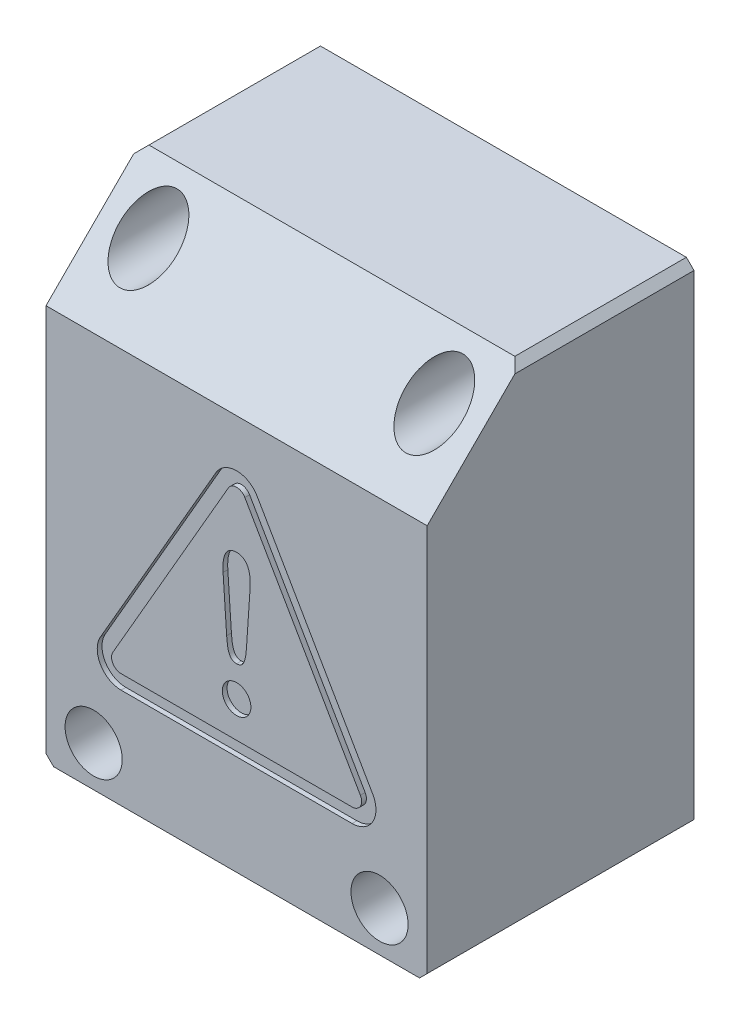
SolidWorks part; units mm, degrees
ref_plane "Front Plane" through (0, 0, 0) normal (0, 0, 1) x (1, 0, 0)
ref_plane "Top Plane" through (0, 0, 0) normal (0, 1, 0) x (1, 0, 0)
ref_plane "Right Plane" through (0, 0, 0) normal (1, 0, 0) x (0, 0, -1)
ref_plane "Plane1" through (19.8609, 0, 0) normal (1, 0, 0) x (0, 0, -1)
sketch "Sketch1" plane through (19.8609, 0, 0) normal (1, 0, 0) x (0, 0, -1)
  line L0 (0.0201, -25.9091) -> (0.0201, 25.5909)
  line L1 (0.0201, 25.5909) -> (-17.9799, 25.5909)
  line L2 (-17.9799, 25.5909) -> (-27.9799, 15.5909)
  line L3 (-27.9799, 15.5909) -> (-27.9799, -25.9091)
  line L4 (-27.9799, -25.9091) -> (0.0201, -25.9091)
  dimension "D1" = 10
  dimension "D2" = 28
  dimension "D3" = 41.5
  dimension "D4" = 51.5
extrude "Boss-Extrude1" add sketch "Sketch1" against normal blind 40
ref_plane "Plane2" through (-19.1391, 0, 0) normal (-1, 0, 0) x (0, -1, 0)
sketch "Sketch2" plane through (-19.1391, 0, 0) normal (-1, 0, 0) x (0, -1, 0)
  line L0 (-24.5909, 17.5657) -> (-24.5909, -0.0201)
  line L1 (-24.5909, -0.0201) -> (24.9091, -0.0201)
  line L2 (24.9091, -0.0201) -> (24.9091, 26.9799)
  line L3 (24.9091, 26.9799) -> (-15.1767, 26.9799)
  line L4 (-15.1767, 26.9799) -> (-24.5909, 17.5657)
  dimension "D1" = 9.4142
  dimension "D2" = 49.5
  dimension "D3" = 17.5858
  dimension "D4" = 27
extrude "Cut-Extrude1" cut sketch "Sketch2" against normal blind 38
sketch "Sketch3" plane through (18.8609, 0, 0) normal (-1, 0, 0) x (0, 0, 1)
  line L0 (-0.0201, 10.3409) -> (-0.0201, 3.8409)
  line L1 (-0.0201, 3.8409) -> (18.9799, 3.8409)
  line L2 (18.9799, 3.8409) -> (18.9799, 10.3409)
  line L3 (18.9799, 10.3409) -> (-0.0201, 10.3409)
  line L5 (17.5657, 24.5909) -> (-0.0201, 24.5909) construction
  line L6 (-0.0201, 24.5909) -> (-0.0201, -24.9091) construction
  dimension "D1" = 19
  dimension "D2" = 14.25
  dimension "D3" = 20.75
extrude "Cut-Extrude2" [suppressed] cut sketch "Sketch3" against normal through all
sketch "Sketch4" plane through (-20.1391, 0, 0) normal (-1, 0, 0) x (0, 0, 1)
  line L0 (-0.0201, 3.8409) -> (18.9799, 3.8409)
  line L1 (18.9799, 3.8409) -> (18.9799, 10.3409)
  line L2 (18.9799, 10.3409) -> (-0.0201, 10.3409)
  line L3 (-0.0201, 10.3409) -> (-0.0201, 3.8409)
  line L4 (27.9799, -25.9091) -> (-0.0201, -25.9091) construction
  line L5 (27.9799, 15.5909) -> (27.9799, -25.9091) construction
  dimension "D1" = 9
  dimension "D2" = 28
  dimension "D3" = 29.75
  dimension "D4" = 36.25
extrude "Cut-Extrude3" [suppressed] cut sketch "Sketch4" against normal through all
ref_plane "Plane3" through (0, 21.0783, 21.0783) normal (0, 0.7071, 0.7071) x (-1, 0, 0)
ref_plane "Plane4" through (0, 0, 7.9799) normal (0, 0, -1) x (-1, 0, 0)
sketch "Sketch6" plane through (0, 0, 7.9799) normal (0, 0, -1) x (-1, 0, 0)
  line L0 (19.1391, 24.5909) -> (11.1391, 24.5909)
  line L1 (11.1391, 24.5909) -> (11.1391, 17.3409)
  line L2 (11.1391, 17.3409) -> (19.1391, 17.3409)
  line L3 (19.1391, 17.3409) -> (19.1391, 24.5909)
  dimension "D1" = 8
  dimension "D2" = 7.25
extrude "Boss-Extrude2" add sketch "Sketch6" against normal up to surface up to plane "Plane3"
sketch "Sketch7" plane through (0, 0, 7.9799) normal (0, 0, -1) x (-1, 0, 0)
  line L0 (-18.8609, 24.5909) -> (-18.8609, 17.3409)
  line L1 (-18.8609, 17.3409) -> (-10.8609, 17.3409)
  line L2 (-10.8609, 17.3409) -> (-10.8609, 24.5909)
  line L3 (-10.8609, 24.5909) -> (-18.8609, 24.5909)
  dimension "D1" = 8
  dimension "D2" = 7.25
extrude "Boss-Extrude3" add sketch "Sketch7" against normal up to next
sketch "Sketch8" plane through (0, 0, 26.9799) normal (0, 0, -1) x (-1, 0, 0)
  line L0 (-10.8609, -24.9091) -> (-18.8609, -24.9091)
  line L1 (-18.8609, -24.9091) -> (-18.8609, -17.6591)
  line L2 (-18.8609, -17.6591) -> (-10.8609, -17.6591)
  line L3 (-10.8609, -17.6591) -> (-10.8609, -24.9091)
  line L4 (19.1391, -24.9091) -> (19.1391, 15.1767) construction
  line L5 (-18.8609, 15.1767) -> (19.1391, 15.1767) construction
  dimension "D1" = 30
  dimension "D2" = 38
  dimension "D3" = 32.8358
  dimension "D4" = 40.0858
extrude "Boss-Extrude4" add sketch "Sketch8" along normal blind 19
sketch "Sketch9" plane through (0, 0, 26.9799) normal (0, 0, -1) x (-1, 0, 0)
  line L0 (19.1391, -17.6591) -> (19.1391, -24.9091)
  line L1 (19.1391, -24.9091) -> (11.1391, -24.9091)
  line L2 (11.1391, -24.9091) -> (11.1391, -17.6591)
  line L3 (11.1391, -17.6591) -> (19.1391, -17.6591)
  line L4 (19.1391, -24.9091) -> (19.1391, 15.1767) construction
  line L5 (-10.8609, -24.9091) -> (19.1391, -24.9091) construction
  dimension "D1" = 8
  dimension "D2" = 7.25
extrude "Boss-Extrude5" add sketch "Sketch9" along normal blind 19
sketch "Sketch10" plane through (0, 0, 27.9799) normal (0, 0, 1) x (1, 0, 0)
  line L0 (14.1503, -11.6591) -> (2.0259, 9.3409)
  line L1 (-2.3042, 9.3409) -> (-14.4285, -11.6591)
  line L2 (-12.2635, -15.4091) -> (11.9852, -15.4091)
  line L3 (19.8609, 15.5909) -> (19.8609, -25.9091) construction
  line L4 (-20.1391, 15.5909) -> (19.8609, 15.5909) construction
  arc A0 (11.9852, -15.4091) -> (14.1503, -11.6591) centre (11.9852, -12.9091) ccw
  arc A1 (2.0259, 9.3409) -> (-2.3042, 9.3409) centre (-0.1391, 8.0909) ccw
  arc A2 (-14.4285, -11.6591) -> (-12.2635, -15.4091) centre (-12.2635, -12.9091) ccw
  dimension "D1" = 2.5
  dimension "D2" = 2.5
  dimension "D3" = 5.7106
  dimension "D4" = 7.8756
  dimension "D5" = 17.8349
  dimension "D6" = 6.25
extrude "Cut-Extrude4" cut sketch "Sketch10" against normal blind 0.5
sketch "Sketch11" plane through (0, 0, 27.4799) normal (0, 0, 1) x (1, 0, 0)
  line L0 (-13.1295, -12.4091) -> (-1.0052, 8.5909)
  line L1 (0.7269, 8.5909) -> (12.8513, -12.4091)
  line L2 (11.9852, -13.9091) -> (-12.2635, -13.9091)
  arc A0 (-1.0052, 8.5909) -> (0.7269, 8.5909) centre (-0.1391, 8.0909) cw
  arc A1 (12.8513, -12.4091) -> (11.9852, -13.9091) centre (11.9852, -12.9091) cw
  arc A2 (-12.2635, -13.9091) -> (-13.1295, -12.4091) centre (-12.2635, -12.9091) cw
  dimension "D1" = 1
  dimension "D2" = 1
  dimension "D3" = 1.299
  dimension "D4" = 2.1651
  dimension "D5" = 14.2894
  dimension "D6" = 0.75
extrude "Boss-Extrude6" add sketch "Sketch11" along normal blind 0.5
ref_plane "Plane5" through (0, 0, 26.4799) normal (0, 0, 1) x (1, 0, 0)
sketch "Sketch12" plane through (0, 0, 26.4799) normal (0, 0, 1) x (1, 0, 0)
  line L0 (-1.1818, -4.92) -> (-1.5574, 0.6422)
  line L1 (1.2791, 0.6422) -> (0.9035, -4.92)
  spline S0 degree 3 poles (-1.5574, 0.6422) (-1.5623, 0.7269) (-1.572, 0.8961) (-1.5736, 1.1504) (-1.5635, 1.4044) (-1.5395, 1.6575) (-1.4986, 1.9084) (-1.436, 2.155) (-1.3478, 2.3942) (-1.2279, 2.6201) (-1.0702, 2.8215) (-0.8738, 2.9864) (-0.6445, 3.1009) (-0.3955, 3.1666) (-0.2248, 3.1736) (-0.1391, 3.1771) knots 0 0 0 0 0.076934 0.153716 0.23049 0.30738 0.384178 0.460862 0.537778 0.614836 0.691826 0.768406 0.845421 0.922433 1 1 1 1
  spline S1 degree 3 poles (-0.1391, 3.1771) (-0.0655, 3.1745) (0.0814, 3.1695) (0.2981, 3.1217) (0.5034, 3.0377) (0.689, 2.9145) (0.8467, 2.7573) (0.9749, 2.5757) (1.0751, 2.3781) (1.1517, 2.1705) (1.2085, 1.957) (1.2488, 1.7403) (1.2753, 1.5222) (1.2903, 1.303) (1.2954, 1.083) (1.2921, 0.8626) (1.2834, 0.7157) (1.2791, 0.6422) knots 0 0 0 0 0.06669 0.133119 0.19992 0.266795 0.333669 0.400734 0.467442 0.534072 0.600968 0.667508 0.733796 0.800116 0.866607 0.933255 1 1 1 1
  spline S2 degree 3 poles (0.9035, -4.92) (0.899, -4.9847) (0.89, -5.114) (0.8736, -5.3078) (0.8534, -5.5013) (0.8284, -5.6943) (0.7967, -5.8864) (0.7549, -6.0766) (0.7007, -6.2637) (0.6289, -6.4449) (0.5329, -6.6149) (0.4053, -6.7638) (0.2432, -6.8747) (0.0564, -6.939) (-0.0737, -6.9455) (-0.1391, -6.9488) knots 0 0 0 0 0.076937 0.153837 0.230708 0.307639 0.384652 0.461589 0.538535 0.615507 0.692327 0.76911 0.845963 0.922602 1 1 1 1
  spline S3 degree 3 poles (-0.1391, -6.9488) (-0.2042, -6.9456) (-0.3345, -6.9393) (-0.5217, -6.8747) (-0.6846, -6.7631) (-0.8124, -6.6132) (-0.9083, -6.4425) (-0.9801, -6.2606) (-1.034, -6.0733) (-1.0756, -5.8833) (-1.1071, -5.6919) (-1.1318, -5.4998) (-1.1519, -5.3069) (-1.1683, -5.1136) (-1.1773, -4.9845) (-1.1818, -4.92) knots 0 0 0 0 0.076984 0.154213 0.231303 0.308509 0.385703 0.462682 0.539884 0.616678 0.69328 0.76987 0.84651 0.923222 1 1 1 1
  dimension "D1" = 0.0035
  dimension "D2" = 0.0053
  dimension "D3" = 0.0149
  dimension "D4" = 0.0206
  dimension "D5" = 0.0475
  dimension "D6" = 0.0882
  dimension "D7" = 0.1457
  dimension "D8" = 0.2228
  dimension "D9" = 0.3235
  dimension "D10" = 0.3905
  dimension "D11" = 0.4045
  dimension "D12" = 0.421
  dimension "D13" = 0.4414
  dimension "D14" = 0.4523
  dimension "D15" = 0.4667
  dimension "D16" = 0.499
  dimension "D17" = 0.5411
  dimension "D18" = 0.5962
  dimension "D19" = 0.6097
  dimension "D20" = 0.6692
  dimension "D21" = 0.7664
  dimension "D22" = 0.7941
  dimension "D23" = 0.8944
  dimension "D24" = 0.9982
  dimension "D25" = 1.055
  dimension "D26" = 1.213
  dimension "D27" = 1.2383
  dimension "D28" = 1.4331
  dimension "D29" = 1.6269
  dimension "D30" = 1.689
  dimension "D31" = 1.8117
  dimension "D32" = 1.9354
  dimension "D33" = 1.9727
  dimension "D34" = 2.1011
  dimension "D35" = 2.1627
  dimension "D36" = 2.1984
  dimension "D37" = 2.2711
  dimension "D38" = 2.3261
  dimension "D39" = 2.3574
  dimension "D40" = 2.368
  dimension "D41" = 2.4
  dimension "D42" = 2.4251
  dimension "D43" = 2.4453
  dimension "D44" = 2.4618
  dimension "D45" = 2.4758
  dimension "D46" = 2.5156
  dimension "D47" = 2.6366
  dimension "D48" = 2.7258
  dimension "D49" = 2.789
  dimension "D50" = 2.8307
  dimension "D51" = 2.8514
  dimension "D52" = 2.8552
  dimension "D53" = 2.8638
  dimension "D54" = 2.8657
  dimension "D55" = 0.0187
  dimension "D56" = 0.0191
  dimension "D57" = 0.0819
  dimension "D58" = 0.082
  dimension "D59" = 0.1914
  dimension "D60" = 0.192
  dimension "D61" = 0.3374
  dimension "D62" = 0.3391
  dimension "D63" = 0.5056
  dimension "D64" = 0.5084
  dimension "D65" = 0.6861
  dimension "D66" = 0.689
  dimension "D67" = 0.8727
  dimension "D68" = 0.8763
  dimension "D69" = 1.0627
  dimension "D70" = 1.066
  dimension "D71" = 1.2548
  dimension "D72" = 1.2571
  dimension "D73" = 1.4477
  dimension "D74" = 1.4491
  dimension "D75" = 1.641
  dimension "D76" = 1.6419
  dimension "D77" = 1.8348
  dimension "D78" = 1.8352
  dimension "D79" = 2.0289
  dimension "D80" = 7.591
  dimension "D81" = 7.8116
  dimension "D82" = 7.8452
  dimension "D83" = 8.032
  dimension "D84" = 8.0992
  dimension "D85" = 8.252
  dimension "D86" = 8.3529
  dimension "D87" = 8.4709
  dimension "D88" = 8.6061
  dimension "D89" = 8.6885
  dimension "D90" = 8.8567
  dimension "D91" = 8.9049
  dimension "D92" = 9.1023
  dimension "D93" = 9.1186
  dimension "D94" = 9.3251
  dimension "D95" = 9.3406
  dimension "D96" = 9.5215
  dimension "D97" = 9.5649
  dimension "D98" = 9.7022
  dimension "D99" = 9.7646
  dimension "D100" = 9.8577
  dimension "D101" = 9.9266
  dimension "D102" = 9.98
  dimension "D103" = 10.0416
  dimension "D104" = 10.0646
  dimension "D105" = 10.1062
  dimension "D106" = 10.1116
  dimension "D107" = 10.1259
extrude "Cut-Extrude5" cut sketch "Sketch12" against normal blind 0.5 from surface at 1.5 starting at face at (-0.1391, -5.9091, 27.9799)
hole_wizard "#3 Clearance Hole1" positions "Sketch14" profile "Sketch13" hole size "#3" standard "ANSI Inch"
sketch "Sketch14" plane through (0, 0, 27.9799) normal (0, 0, 1) x (1, 0, 0)
  point P0 (-0.1391, -10.1591)
sketch "Sketch13" plane through (-0.1391, -10.1591, 27.9799) normal (1, 0, 0) x (0, -1, 0)
  line L0 (0, 0) -> (0, 0.5)
  line L1 (0, 0.5) -> (1.5, 0.5)
  line L2 (1.5, 0.5) -> (1.5, 0)
  line L5 (1.5, 0) -> (0, 0)
  line L10 (0, 0.5) -> (-1.5, 0.5) construction
  line L11 (0, -6.35) -> (0, 107.95) construction
  dimension "Hole Dia." = 3
  dimension "Hole Depth" = 0.5
  dimension "Drill Angle" = 180
hole_wizard "CBORE for #4 Binding Head Machine Screw1" positions "Sketch16" profile "Sketch15" counterbore size "#4" standard "ANSI Inch"
sketch "Sketch16" plane through (0, 0, 27.9799) normal (0, 0, 1) x (1, 0, 0)
  point P0 (14.8609, -21.6591)
  point P1 (-15.1391, -21.6591)
sketch "Sketch15" plane through (14.8609, -21.6591, 27.9799) normal (1, 0, 0) x (0, -1, 0)
  line L0 (0, 0) -> (0, 28)
  line L1 (0, 28) -> (1.6, 28)
  line L3 (1.6, 28) -> (1.6, 19)
  line L4 (1.6, 19) -> (3, 19)
  line L5 (3, 19) -> (3, 0)
  line L7 (3, 0) -> (0, 0)
  line L11 (0, -6.35) -> (0, 107.95) construction
  dimension "Thru Hole Dia." = 3.2
  dimension "Thru Hole Depth" = 28
  dimension "C'Bore Dia." = 6
  dimension "C'Bore Depth" = 19
ref_plane "Plane6" through (0, 0, 25.2299) normal (0, 0, 1) x (1, 0, 0)
hole_wizard "CBORE for #4 Binding Head Machine Screw2" positions "Sketch18" profile "Sketch17" counterbore size "#4" standard "ANSI Inch"
sketch "Sketch18" plane through (0, 0, 25.2299) normal (0, 0, 1) x (1, 0, 0)
  point P0 (-15.1391, 21.3409)
  point P1 (14.8609, 21.3409)
sketch "Sketch17" plane through (-15.1391, 21.3409, 25.2299) normal (1, 0, 0) x (0, -1, 0)
  line L0 (0, 0) -> (0, 25.25)
  line L1 (0, 25.25) -> (1.6, 25.25)
  line L3 (1.6, 25.25) -> (1.6, 16.25)
  line L4 (1.6, 16.25) -> (3, 16.25)
  line L5 (3, 16.25) -> (3, 0)
  line L7 (3, 0) -> (0, 0)
  line L11 (0, -6.35) -> (0, 107.95) construction
  dimension "Thru Hole Dia." = 3.2
  dimension "Thru Hole Depth" = 25.25
  dimension "C'Bore Dia." = 6
  dimension "C'Bore Depth" = 16.25
chamfer "Chamfer2" distance 0.8 angle 45 4 edges at (-20.1391, 25.5909, 8.9799) (19.8609, -25.9091, 13.9799) (-20.1391, -25.9091, 13.9799) (19.8609, 25.5909, 8.9799)
chamfer "Chamfer1" [suppressed] distance 0.25 angle 45
fillet "Fillet1" radius 1 8 edges at (18.8609, -17.6591, 17.4799) (-19.1391, 17.3409, 16.3978) (-19.1391, -17.6591, 17.4799) (-11.1391, -24.9091, 17.4799) (10.8609, -24.9091, 17.4799) (-11.1391, 24.5909, 12.7728) (10.8609, 24.5909, 12.7728) (18.8609, 17.3409, 16.3978)
fillet "Fillet2" radius 4 4 edges at (10.8609, -17.6591, 17.4799) (10.8609, 17.3409, 16.3978) (-11.1391, 17.3409, 16.3978) (-11.1391, -17.6591, 17.4799)
